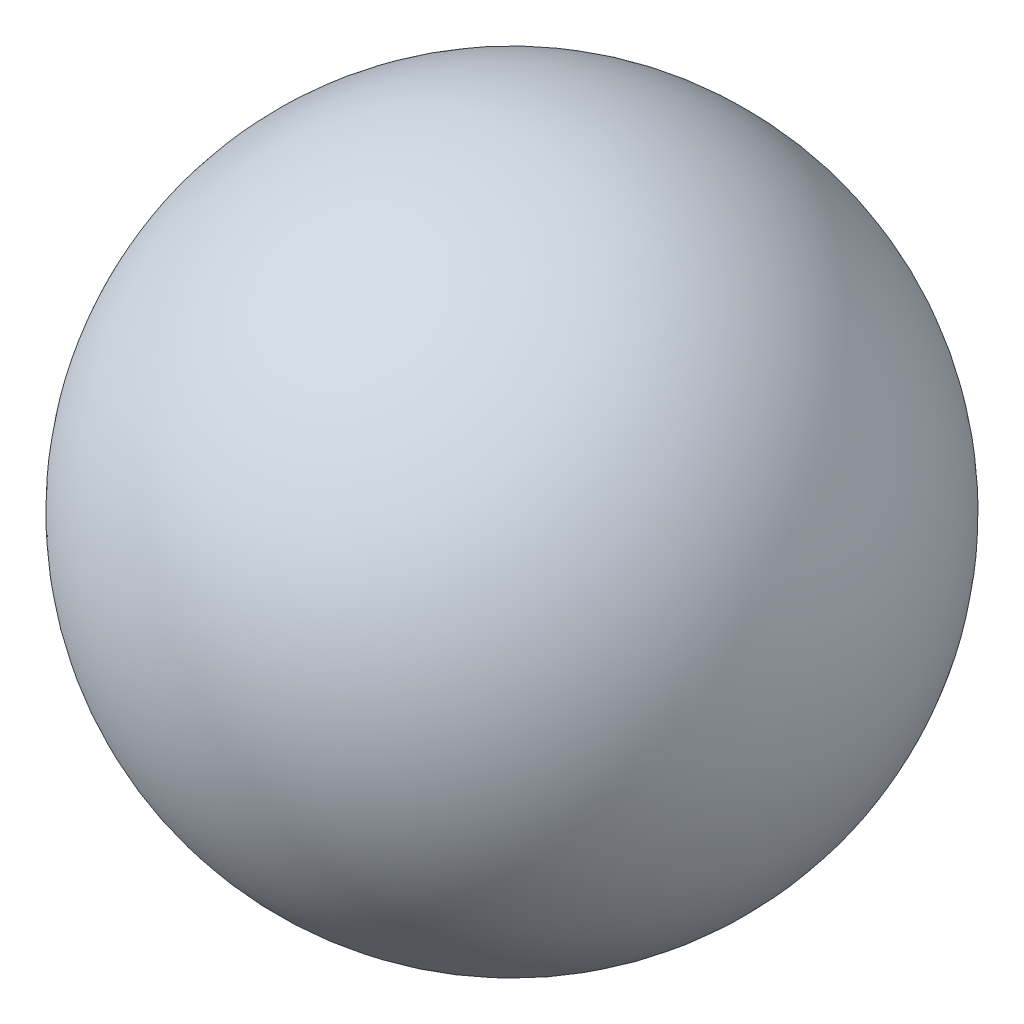
SolidWorks part; units mm, degrees
ref_plane "Plan1" through (0, 0, 0) normal (0, 0, 1) x (1, 0, 0)
ref_plane "Plan2" through (0, 0, 0) normal (0, 1, 0) x (1, 0, 0)
ref_plane "Plan3" through (0, 0, 0) normal (1, 0, 0) x (0, 0, -1)
sketch "Esquisse1" plane through (0, 0, 0) normal (0, 0, 1) x (1, 0, 0)
  line L0 (0.75, 3.25) -> (3.25, 3.25)
  line L1 (2, 3.25) -> (4.3947, 3.25) construction
  circle A0 centre (2, 3.25) radius 1.25 construction
  arc A1 (3.25, 3.25) -> (0.75, 3.25) centre (2, 3.25) ccw
revolve "Base-Révolution" add sketch "Esquisse1" angle 360 about L1
